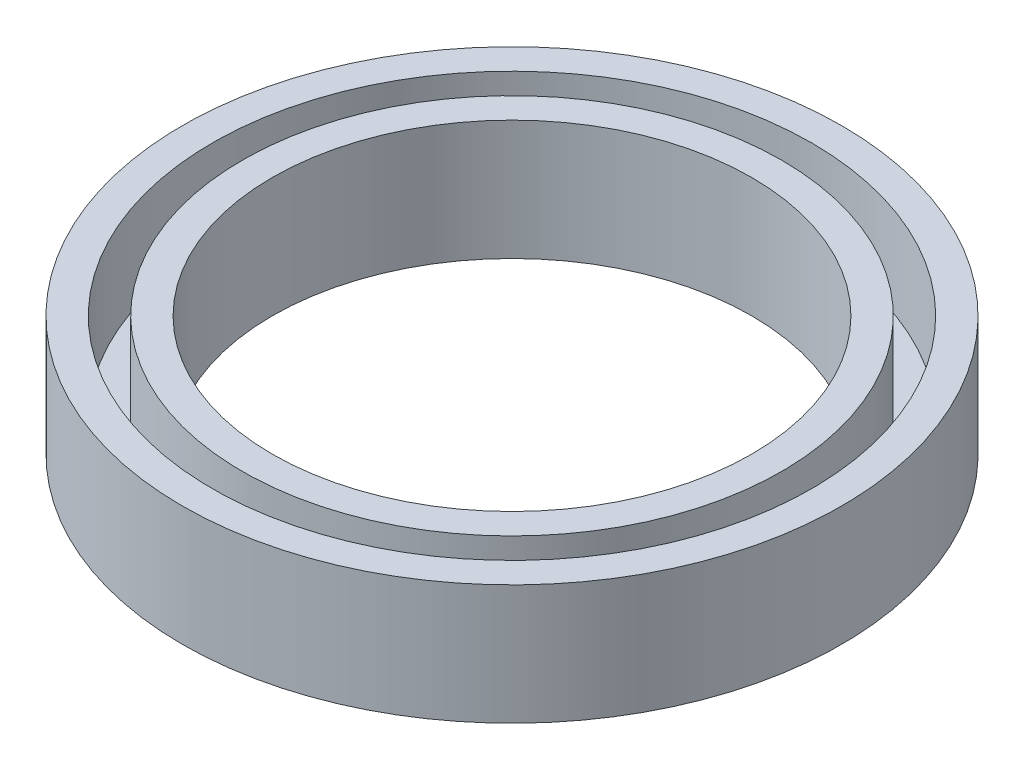
SolidWorks part; units mm, degrees
material "PTFE (general)"
ref_plane "Front" through (0, 0, 0) normal (0, 0, 1) x (1, 0, 0)
ref_plane "Top" through (0, 0, 0) normal (0, 1, 0) x (1, 0, 0)
ref_plane "Right" through (0, 0, 0) normal (1, 0, 0) x (0, 0, -1)
sketch "Sketch1" plane through (0, 0, 0) normal (0, 0, 1) x (1, 0, 0)
  line L0 (-8.7312, 3.175) -> (-8.7312, 0)
  line L1 (-8.7312, 0) -> (-6.35, 0)
  line L2 (-6.35, 0) -> (-6.35, 3.175)
  line L3 (-6.35, 3.175) -> (-7.1437, 3.175)
  line L4 (-7.1437, 3.175) -> (-7.1437, 0.7938)
  line L5 (-7.1437, 0.7938) -> (-7.9375, 0.7937)
  line L6 (-7.9375, 0.7937) -> (-7.9375, 3.175)
  line L7 (-7.9375, 3.175) -> (-8.7312, 3.175)
  line L8 (0, 0) -> (0, 3.175) construction
  dimension "D1" = 8.7312
  dimension "D2" = 3.175
  dimension "D3" = 6.35
  dimension "D4" = 0.7937
  dimension "D5" = 0.7937
revolve "Revolve1" add sketch "Sketch1" angle 360 about L8
equation "\"D5@Sketch1\"=\"D4@Sketch1\""
